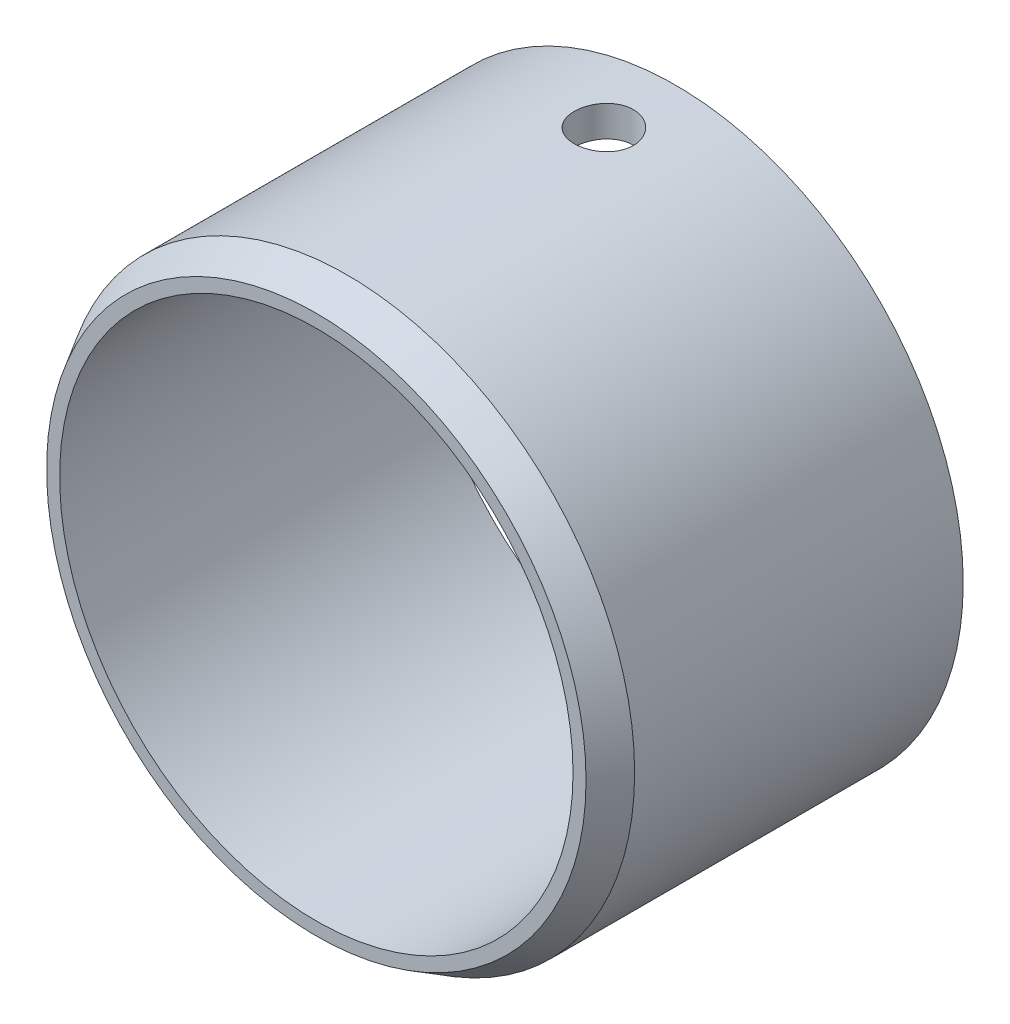
SolidWorks part; units mm, degrees
ref_plane "Front Plane" through (0, 0, 0) normal (0, 0, 1) x (1, 0, 0)
ref_plane "Top Plane" through (0, 0, 0) normal (0, 1, 0) x (1, 0, 0)
ref_plane "Right Plane" through (0, 0, 0) normal (1, 0, 0) x (0, 0, -1)
sketch "Sketch1" plane through (0, 0, 0) normal (0, 0, 1) x (1, 0, 0)
  circle A0 centre (0, 0) radius 15.875
  circle A1 centre (0, 0) radius 17.78
  dimension "D1" = 31.75
  dimension "D2" = 1.905
extrude "Boss-Extrude1" add sketch "Sketch1" along normal blind 22.225
chamfer "Chamfer4" distance 1.905 angle 30 1 edges at (17.78, 0, 22.225)
sketch "Sketch2" plane through (0, 0, 22.225) normal (0, 0, 1) x (1, 0, 0)
  circle A0 centre (0, 0) radius 14.605
  dimension "D1" = 29.21
extrude "Cut-Extrude1" [suppressed] cut sketch "Sketch2" against normal blind 1.27 flip side to cut
chamfer "Chamfer2" [suppressed] distance 1.27 angle 30
hole_wizard "#27 (0.144) Diameter Hole1" positions "3DSketch2" profile "Sketch4" hole size "#27" standard "ANSI Inch"
sketch3d "3DSketch2"
  point P11 (0, 17.78, 4.445)
sketch "Sketch4" plane through (0, 17.78, 4.445) normal (1, 0, 0) x (0, 0, 1)
  line L0 (0, 0) -> (0, 26.4989)
  line L1 (0, 26.4989) -> (1.8288, 25.4)
  line L2 (1.8288, 25.4) -> (1.8288, 0)
  line L5 (1.8288, 0) -> (0, 0)
  line L10 (0, 26.4989) -> (-1.8288, 25.4) construction
  line L11 (0, -6.35) -> (0, 107.95) construction
  dimension "Hole Dia." = 3.6576
  dimension "Hole Depth" = 25.4
  dimension "Drill Angle" = 118
sketch "Sketch5" [suppressed] plane through (0, 0, 10.16) normal (0, 0, 1) x (1, 0, 0)
  circle A0 centre (0, 0) radius 15.24
  dimension "D1" = 30.48
extrude "Boss-Extrude2" [suppressed] add sketch "Sketch5" along normal blind 1.905
sketch "Sketch6" [suppressed] plane through (0, 0, 12.065) normal (0, 0, 1) x (1, 0, 0)
  circle A0 centre (0, 0) radius 10.795
  dimension "D1" = 21.59
extrude "Cut-Extrude2" [suppressed] cut sketch "Sketch6" against normal through all
sketch "Sketch7" [suppressed] plane through (0, 0, 12.065) normal (0, 0, 1) x (1, 0, 0)
  circle A0 centre (0, 0) radius 12.065
  circle A1 centre (0, 0) radius 10.795
  dimension "D1" = 1.27
  dimension "D2" = 24.13
extrude "Boss-Extrude3" [suppressed] add sketch "Sketch7" along normal blind 10.16
